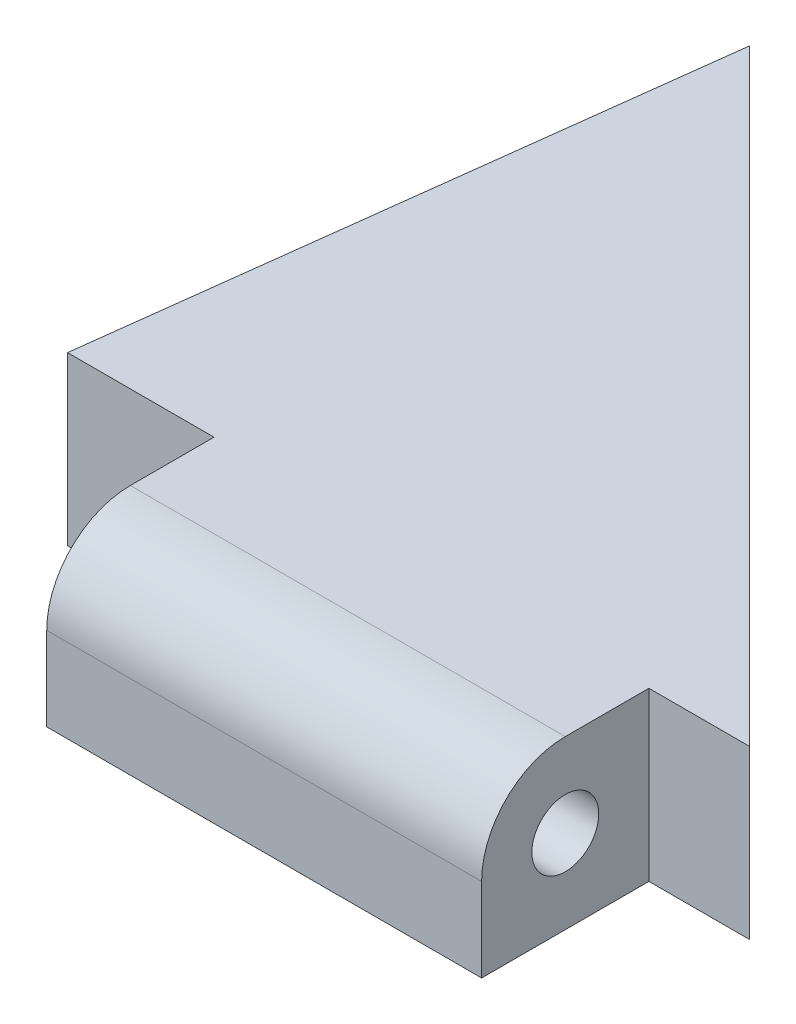
SolidWorks part; units mm, degrees
material "ABS PC"
ref_plane "Front Plane" through (0, 0, 0) normal (0, 0, 1) x (1, 0, 0)
ref_plane "Top Plane" through (0, 0, 0) normal (0, 1, 0) x (1, 0, 0)
ref_plane "Right Plane" through (0, 0, 0) normal (1, 0, 0) x (0, 0, -1)
sketch "Sketch1" plane through (0, 0, 0) normal (0, 1, 0) x (1, 0, 0)
  line L0 (-25.881, 0) -> (-23.0208, 23.0208)
  line L1 (-23.0208, 23.0208) -> (0, 0)
  line L2 (0, 0) -> (-25.881, 0)
  dimension "D1" = 45
  dimension "D2" = 25.881
  dimension "D3" = 82.917
  dimension "D4" = 0
  dimension "D5" = 0
extrude "Boss-Extrude1" add sketch "Sketch1" along normal blind 6.35
sketch "Sketch2" plane through (0, 0, 0) normal (1, 0, 0) x (0, 0, -1)
  line L0 (0, 6.35) -> (0, 0) construction
  line L1 (0, 6.35) -> (23.0208, 6.35) construction
  line L2 (-6.35, 0) -> (0, 0)
  line L3 (-6.35, 0) -> (-6.35, 6.35)
  line L4 (-6.35, 6.35) -> (0, 6.35)
  line L5 (0, 0) -> (0, 6.35)
  line L6 (-6.35, 0) -> (0, 6.35) construction
  line L7 (-6.35, 6.35) -> (0, 0) construction
  circle A0 centre (-3.175, 3.175) radius 3.175
  circle A1 centre (-3.175, 3.175) radius 1.27
  point P5 (0, 3.175)
  dimension "D1" = 6.35
  dimension "D4" = 2.54
  dimension "D2" = 3.175
  dimension "D3" = 0
extrude "Boss-Extrude2" add sketch "Sketch2" against normal blind 16.51 from offset 3.81 contours A0 A1 | A0 L5 L4 | A0 L2 L5 | A0 L3 L2 offset against normal yes
